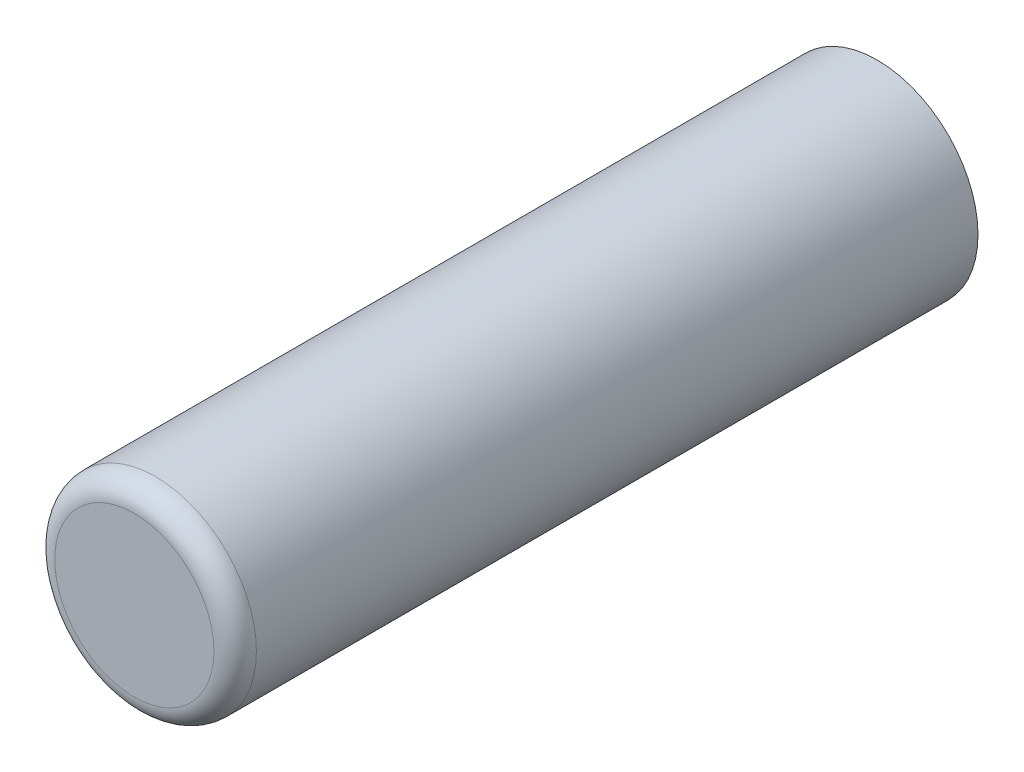
SolidWorks part; units mm, degrees
ref_plane "Front Plane" through (0, 0, 0) normal (0, 0, 1) x (1, 0, 0)
ref_plane "Top Plane" through (0, 0, 0) normal (0, 1, 0) x (1, 0, 0)
ref_plane "Right Plane" through (0, 0, 0) normal (1, 0, 0) x (0, 0, -1)
sketch "Sketch1" plane through (0, 0, 0) normal (0, 0, 1) x (1, 0, 0)
  circle A0 centre (0, 0) radius 3.8
  dimension "D1" = 7.6
extrude "Boss-Extrude1" add sketch "Sketch1" along normal mid plane 28
fillet "Fillet1" radius 0.8 1 edges at (3.8, 0, 14)
